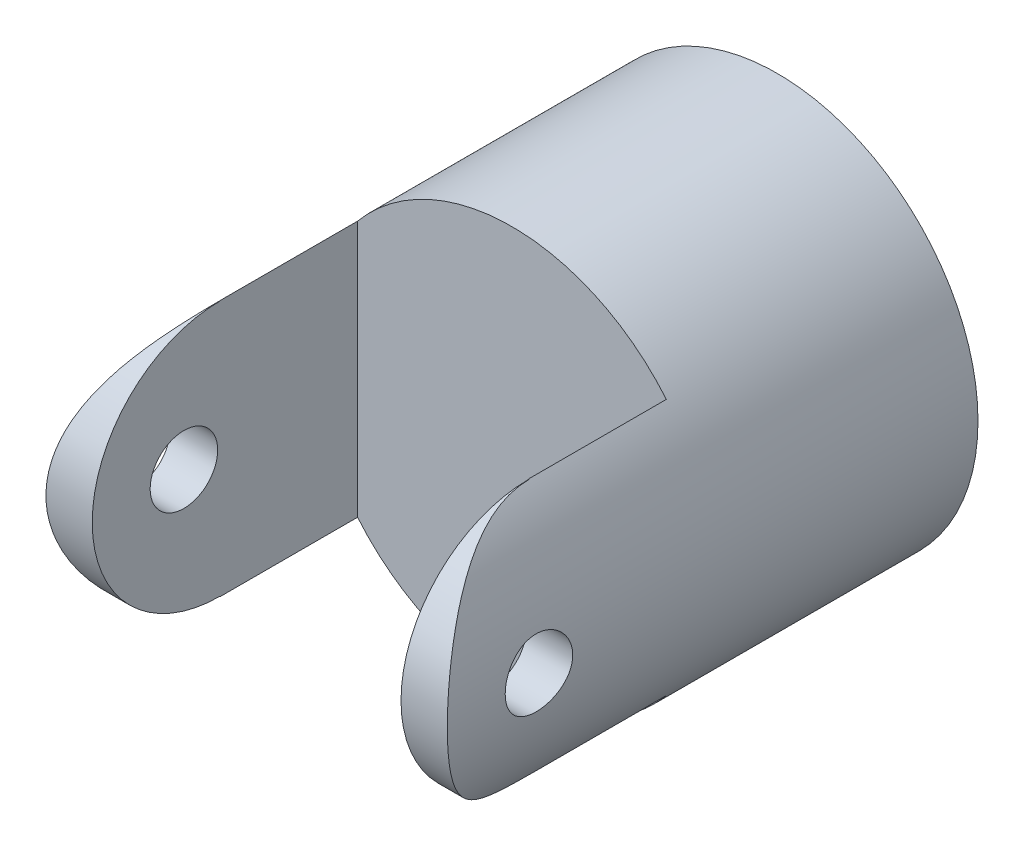
SolidWorks part; units mm, degrees
ref_plane "Front Plane" through (0, 0, 0) normal (0, 0, 1) x (1, 0, 0)
ref_plane "Top Plane" through (0, 0, 0) normal (0, 1, 0) x (1, 0, 0)
ref_plane "Right Plane" through (0, 0, 0) normal (1, 0, 0) x (0, 0, -1)
sketch "Sketch1" plane through (0, 0, 0) normal (0, 0, 1) x (1, 0, 0)
  circle A0 centre (0, 0) radius 4.16
  dimension "D1" = 8.32
extrude "Extrude1" add sketch "Sketch1" along normal blind 11
sketch "Sketch2" plane through (0, 0, 0) normal (0, 1, 0) x (1, 0, 0)
  line L0 (-4.16, 0) -> (-4.16, -11) construction
  line L1 (-3.2, -11.8574) -> (3.2, -11.8574)
  line L2 (-3.2, -11.8574) -> (-3.2, -5.5)
  line L3 (-3.2, -5.5) -> (3.2, -5.5)
  line L4 (3.2, -11.8574) -> (3.2, -5.5)
  line L5 (-4.16, -11) -> (4.16, -11) construction
  dimension "D1" = 6.4
  dimension "D2" = 0.96
  dimension "D3" = 5.5
extrude "Extrude2" cut sketch "Sketch2" against normal through all and the other way through all
sketch "Sketch3" plane through (0, 0, 0) normal (1, 0, 0) x (0, 0, -1)
  line L2 (-8.35, 2.65) -> (-8.35, 3.8367)
  line L4 (-8.35, -4.4922) -> (-12.8222, -4.6052)
  line L5 (-12.8222, -4.6052) -> (-12.8222, 3.8367)
  line L6 (-12.8222, 3.8367) -> (-8.35, 3.8367)
  line L8 (-8.35, -2.65) -> (-8.35, -4.4922)
  arc A0 (-8.35, 2.65) -> (-8.35, -2.65) centre (-8.35, 0) ccw
extrude "Extrude3" cut sketch "Sketch3" against normal through all and the other way through all
sketch "Sketch4" plane through (0, 0, 0) normal (1, 0, 0) x (0, 0, -1)
  circle A0 centre (-9.1, 0) radius 0.7
  dimension "D1" = 1.4
extrude "Extrude4" cut sketch "Sketch4" against normal through all and the other way through all
